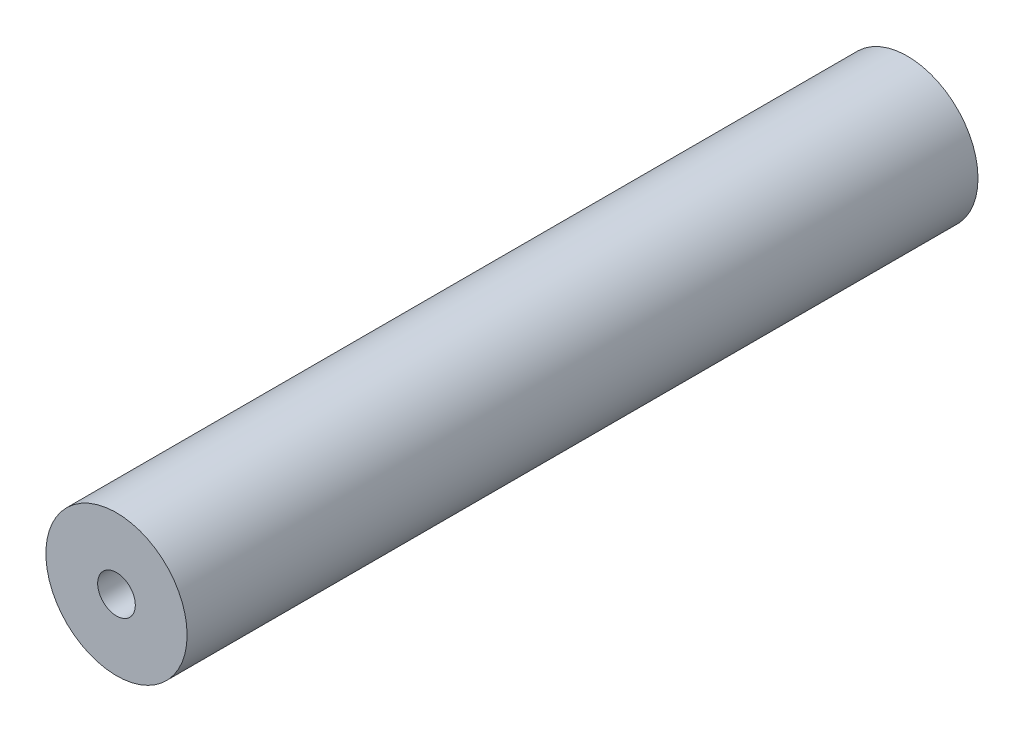
SolidWorks part; units mm, degrees
ref_plane "Front Plane" through (0, 0, 0) normal (0, 0, 1) x (1, 0, 0)
ref_plane "Top Plane" through (0, 0, 0) normal (0, 1, 0) x (1, 0, 0)
ref_plane "Right Plane" through (0, 0, 0) normal (1, 0, 0) x (0, 0, -1)
sketch "Sketch1" plane through (0, 0, 0) normal (0, 0, 1) x (1, 0, 0)
  circle A0 centre (0, 0) radius 9.375
  dimension "D1" = 18.75
extrude "Boss-Extrude1" add sketch "Sketch1" along normal blind 105
ref_point "Point1"
ref_point "Point2"
ref_plane "Plane1" through (0, 0, 52.5) normal (0, 0, -1) x (-1, 0, 0)
sketch "Sketch4" plane through (0, 0, 105) normal (0, 0, 1) x (1, 0, 0)
  circle A0 centre (0, 0) radius 2.5
extrude "Cut-Extrude1" cut sketch "Sketch4" against normal blind 20
mirror "Mirror1" about plane through (0, 0, 52.5) normal (0, 0, -1) of "Cut-Extrude1"
